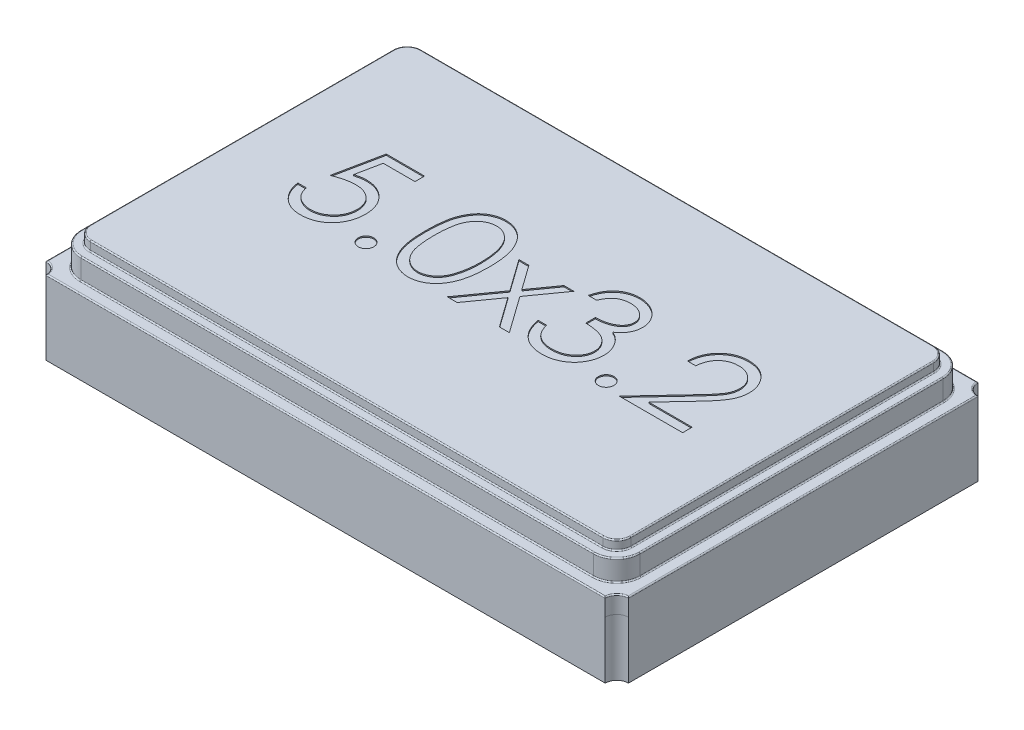
SolidWorks part; units mm, degrees
ref_plane "Front Plane" through (0, 0, 0) normal (0, 0, 1) x (1, 0, 0)
ref_plane "Top Plane" through (0, 0, 0) normal (0, 1, 0) x (1, 0, 0)
ref_plane "Right Plane" through (0, 0, 0) normal (1, 0, 0) x (0, 0, -1)
sketch "Sketch1" plane through (0, 0, 0) normal (0, 1, 0) x (1, 0, 0)
  line L0 (2.5, -1.6) -> (-2.5, 1.6) construction
  line L1 (-2.4, 1.6) -> (2.4, 1.6)
  line L2 (-2.5, 1.5) -> (-2.5, -1.5)
  line L3 (-2.4, -1.6) -> (2.4, -1.6)
  line L4 (2.5, 1.5) -> (2.5, -1.5)
  line L5 (2.5, 1.6) -> (2.4, 1.6) construction
  line L6 (2.5, 1.6) -> (2.5, 1.5) construction
  line L7 (-2.4, 1.6) -> (-2.5, 1.6) construction
  line L8 (-2.5, 1.6) -> (-2.5, 1.5) construction
  line L9 (-2.5, 1.5) -> (-2.5, 1.6) construction
  line L10 (-2.5, -1.6) -> (-2.4, -1.6) construction
  arc A0 (2.4, 1.6) -> (2.5, 1.5) centre (2.5, 1.6) ccw
  arc A1 (2.5, -1.5) -> (2.4, -1.6) centre (2.5, -1.6) ccw
  arc A2 (-2.4, -1.6) -> (-2.5, -1.5) centre (-2.5, -1.6) ccw
  arc A3 (-2.5, 1.5) -> (-2.4, 1.6) centre (-2.5, 1.6) ccw
  dimension "D3" = 0.2
  dimension "D1" = 5
  dimension "D2" = 3.2
  dimension "D4" = 3
  dimension "D5" = 4.8
extrude "Boss-Extrude1" add sketch "Sketch1" along normal blind 0.64
sketch "Sketch2" plane through (0, 0.64, 0) normal (0, 1, 0) x (1, 0, 0)
  line L0 (2.4, -1.5) -> (-2.4, 1.5) construction
  line L1 (-2.2, 1.5) -> (2.2, 1.5)
  line L2 (-2.4, 1.3) -> (-2.4, -1.3)
  line L3 (-2.2, -1.5) -> (2.2, -1.5)
  line L4 (2.4, 1.3) -> (2.4, -1.3)
  line L5 (2.4, 1.6) -> (-2.4, 1.6) construction
  line L6 (-2.5, 1.5) -> (-2.5, -1.5) construction
  arc A0 (2.4, -1.3) -> (2.2, -1.5) centre (2.2, -1.3) cw
  arc A1 (-2.2, -1.5) -> (-2.4, -1.3) centre (-2.2, -1.3) cw
  arc A2 (-2.4, 1.3) -> (-2.2, 1.5) centre (-2.2, 1.3) cw
  arc A3 (2.4, 1.3) -> (2.2, 1.5) centre (2.2, 1.3) ccw
  dimension "D3" = 0.2
  dimension "D1" = 0.1
  dimension "D2" = 0.1
extrude "Boss-Extrude2" add sketch "Sketch2" along normal blind 0.18
sketch "Sketch4" plane through (0, 0.82, 0) normal (0, 1, 0) x (1, 0, 0)
  line L12 (2.32, -1.3) -> (2.32, 1.3)
  line L13 (2.2, 1.42) -> (-2.2, 1.42)
  line L14 (-2.32, 1.3) -> (-2.32, -1.3)
  line L15 (-2.2, -1.42) -> (2.2, -1.42)
  line L16 (2.32, -1.3) -> (2.32, 1.3)
  line L17 (2.2, 1.42) -> (-2.2, 1.42)
  line L18 (-2.32, 1.3) -> (-2.32, -1.3)
  line L19 (-2.2, -1.42) -> (2.2, -1.42)
  arc A12 (2.2, -1.42) -> (2.32, -1.3) centre (2.2, -1.3) ccw
  arc A13 (2.32, 1.3) -> (2.2, 1.42) centre (2.2, 1.3) ccw
  arc A14 (-2.2, 1.42) -> (-2.32, 1.3) centre (-2.2, 1.3) ccw
  arc A15 (-2.32, -1.3) -> (-2.2, -1.42) centre (-2.2, -1.3) ccw
  arc A16 (2.2, -1.42) -> (2.32, -1.3) centre (2.2, -1.3) ccw
  arc A17 (2.32, 1.3) -> (2.2, 1.42) centre (2.2, 1.3) ccw
  arc A18 (-2.2, 1.42) -> (-2.32, 1.3) centre (-2.2, 1.3) ccw
  arc A19 (-2.32, -1.3) -> (-2.2, -1.42) centre (-2.2, -1.3) ccw
  dimension "D1" = 0.08
extrude "Boss-Extrude3" add sketch "Sketch4" along normal blind 0.08
sketch "Sketch5" plane through (0, 0, 0) normal (0, -1, 0) x (1, 0, 0)
  line L0 (-2.33, 1.6) -> (-2.4, 1.6)
  line L1 (-2.5, 1.5) -> (-2.5, 1.43)
  line L2 (-2.3451, 1.53) -> (-1.3, 1.53)
  line L3 (-1.3, 1.53) -> (-1.3, 1)
  line L4 (-1.3, 1) -> (-1.6, 0.7)
  line L5 (-1.6, 0.7) -> (-2.43, 0.7)
  line L6 (-2.43, 0.7) -> (-2.43, 1.4451)
  line L7 (-2.5, -1.5) -> (-2.5, 1.5) construction
  line L8 (-2.4, 1.6) -> (2.4, 1.6) construction
  line L9 (0, 0) -> (0, -0.4357) construction
  line L10 (0, 0) -> (0.4719, 0) construction
  line L11 (2.43, 0.7) -> (2.43, 1.4451)
  line L12 (-2.43, -0.7) -> (-1.3, -0.7)
  line L13 (-1.3, -0.7) -> (-1.3, -1.53)
  line L14 (2.43, 0.7) -> (1.3, 0.7)
  line L15 (2.3451, 1.53) -> (1.3, 1.53)
  line L16 (2.5, 1.5) -> (2.5, 1.43)
  line L17 (2.33, 1.6) -> (2.4, 1.6)
  line L18 (2.33, -1.6) -> (2.4, -1.6)
  line L19 (2.5, -1.5) -> (2.5, -1.43)
  line L20 (2.3451, -1.53) -> (1.3, -1.53)
  line L21 (1.3, -1.53) -> (1.3, -0.7)
  line L22 (1.3, 0.7) -> (1.3, 1.53)
  line L23 (1.3, -0.7) -> (2.43, -0.7)
  line L24 (2.43, -0.7) -> (2.43, -1.4451)
  line L25 (-2.43, -0.7) -> (-2.43, -1.4451)
  line L29 (-2.3451, -1.53) -> (-1.3, -1.53)
  line L30 (-2.5, -1.5) -> (-2.5, -1.43)
  line L31 (-2.33, -1.6) -> (-2.4, -1.6)
  arc A0 (-2.5, 1.43) -> (-2.43, 1.4451) centre (-2.5, 1.6) ccw
  arc A1 (-2.5, 1.5) -> (-2.4, 1.6) centre (-2.5, 1.6) ccw
  arc A2 (-2.5, 1.5) -> (-2.4, 1.6) centre (-2.5, 1.6) ccw construction
  arc A3 (-2.3451, 1.53) -> (-2.33, 1.6) centre (-2.5, 1.6) ccw
  arc A4 (2.3451, 1.53) -> (2.33, 1.6) centre (2.5, 1.6) cw
  arc A5 (2.5, 1.5) -> (2.4, 1.6) centre (2.5, 1.6) cw
  arc A6 (2.5, 1.43) -> (2.43, 1.4451) centre (2.5, 1.6) cw
  arc A7 (2.5, -1.43) -> (2.43, -1.4451) centre (2.5, -1.6) ccw
  arc A8 (2.5, -1.5) -> (2.4, -1.6) centre (2.5, -1.6) ccw
  arc A9 (2.3451, -1.53) -> (2.33, -1.6) centre (2.5, -1.6) ccw
  arc A10 (-2.3451, -1.53) -> (-2.33, -1.6) centre (-2.5, -1.6) cw
  arc A11 (-2.5, -1.5) -> (-2.4, -1.6) centre (-2.5, -1.6) cw
  arc A12 (-2.5, -1.43) -> (-2.43, -1.4451) centre (-2.5, -1.6) cw
  dimension "D7" = 0.07
  dimension "D1" = 1.3
  dimension "D2" = 0.7
  dimension "D3" = 45
  dimension "D4" = 0.3
  dimension "D5" = 0.07
  dimension "D6" = 0.07
split line "Split Line1"
sketch "Sketch6" plane through (0, 0, 1.6) normal (0, 0, 1) x (1, 0, 0)
  line L0 (2.5, 0.64) -> (2.5, 0) construction
  line L1 (2.4, 0.64) -> (2.5, 0.64)
  line L2 (2.4, 0.64) -> (2.4, 0.49)
  line L3 (2.4, 0.49) -> (2.5, 0.49)
  line L4 (2.5, 0.64) -> (2.5, 0.49)
  line L5 (-2.5, 0.64) -> (-2.5, 0) construction
  line L6 (-2.4, 0.64) -> (-2.5, 0.64)
  line L7 (-2.4, 0.64) -> (-2.4, 0.49)
  line L8 (-2.4, 0.49) -> (-2.5, 0.49)
  line L9 (-2.5, 0.64) -> (-2.5, 0.49)
  dimension "D1" = 0.15
split line "Split Line2"
sketch "Sketch7" plane through (0, 0, -1.6) normal (0, 0, -1) x (-1, 0, 0)
  line L0 (2.5, 0.64) -> (2.5, 0) construction
  line L1 (2.4, 0.64) -> (2.5, 0.64)
  line L2 (2.4, 0.64) -> (2.4, 0.49)
  line L3 (2.4, 0.49) -> (2.5, 0.49)
  line L4 (2.5, 0.64) -> (2.5, 0.49)
  line L5 (-2.5, 0.64) -> (-2.5, 0) construction
  line L6 (-2.4, 0.64) -> (-2.5, 0.64)
  line L7 (-2.4, 0.64) -> (-2.4, 0.49)
  line L8 (-2.4, 0.49) -> (-2.5, 0.49)
  line L9 (-2.5, 0.64) -> (-2.5, 0.49)
  dimension "D1" = 0.15
split line "Split Line3"
fillet "Fillet1" radius 0.01 40 edges at (0, 0.9, 1.42) (-2.2849, 0.9, 1.3849) (-2.32, 0.9, 0) (-2.2849, 0.9, -1.3849) (0, 0.9, -1.42) (2.2849, 0.9, -1.3849) (2.32, 0.9, 0) (2.2849, 0.9, 1.3849) (2.32, 0.82, 0) (2.2849, 0.82, -1.3849) (0, 0.82, -1.42) (-2.2849, 0.82, -1.3849) (-2.32, 0.82, 0) (-2.2849, 0.82, 1.3849) (0, 0.82, 1.42) (2.2849, 0.82, 1.3849) (0, 0.82, 1.5) (-2.3414, 0.82, 1.4414) (-2.4, 0.82, 0) (-2.3414, 0.82, -1.4414) (0, 0.82, -1.5) (2.3414, 0.82, -1.4414) (2.4, 0.82, 0) (2.3414, 0.82, 1.4414) (2.3414, 0.64, -1.4414) (0, 0.64, -1.5) (-2.3414, 0.64, -1.4414) (-2.4, 0.64, 0) (-2.3414, 0.64, 1.4414) (0, 0.64, 1.5) (2.3414, 0.64, 1.4414) (2.4, 0.64, 0) (0, 0.64, 1.6) (-2.4293, 0.64, 1.5293) (-2.5, 0.64, 0) (-2.4293, 0.64, -1.5293) (0, 0.64, -1.6) (2.4293, 0.64, -1.5293) (2.5, 0.64, 0) (2.4293, 0.64, 1.5293)
sketch "Sketch8" plane through (0, 0.9, 0) normal (0, 1, 0) x (1, 0, 0)
  text T0 "5.0x3.2" font "Century Gothic" height 0.8
extrude "Cut-Extrude1" cut sketch "Sketch8" against normal blind 0.01
